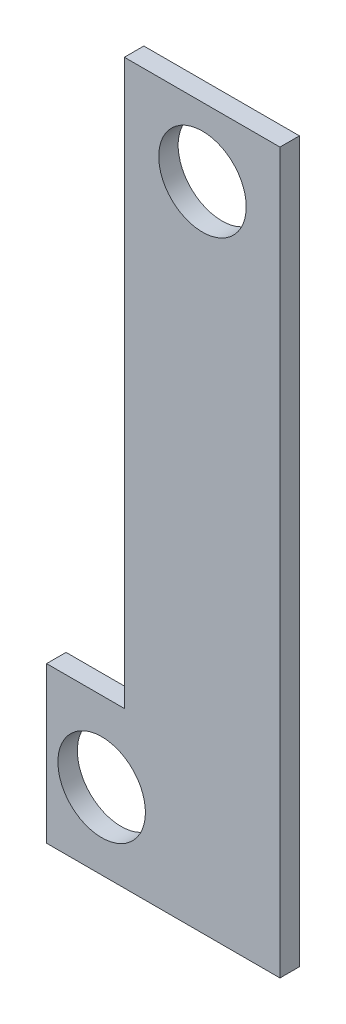
SolidWorks part; units mm, degrees
ref_plane "Front Plane" through (0, 0, 0) normal (0, 0, 1) x (1, 0, 0)
ref_plane "Top Plane" through (0, 0, 0) normal (0, 1, 0) x (1, 0, 0)
ref_plane "Right Plane" through (0, 0, 0) normal (1, 0, 0) x (0, 0, -1)
sketch "Sketch1" plane through (0, 0, 0) normal (0, 0, 1) x (1, 0, 0)
  line L0 (0, 0) -> (76.2, 0)
  line L1 (0, 0) -> (0, 50.8)
  line L2 (0, 50.8) -> (25.4, 50.8)
  line L3 (76.2, 0) -> (76.2, 234.95)
  line L4 (76.2, 234.95) -> (25.4, 234.95)
  line L5 (25.4, 234.95) -> (25.4, 50.8)
  dimension "D1" = 76.2
  dimension "D2" = 50.8
  dimension "D3" = 25.4
  dimension "D4" = 234.95
extrude "Boss-Extrude1" add sketch "Sketch1" along normal blind 6.35 contours L4 L5 L2 L1 L0 L3
sketch "Sketch2" plane through (0, 0, 6.35) normal (0, 0, 1) x (1, 0, 0)
  circle A0 centre (17.9825, 24.8496) radius 14.2875
  circle A1 centre (50.8968, 212.5248) radius 14.2875
  dimension "D1" = 28.575
  dimension "D2" = 28.575
extrude "Cut-Extrude1" cut sketch "Sketch2" against normal blind 6.35
